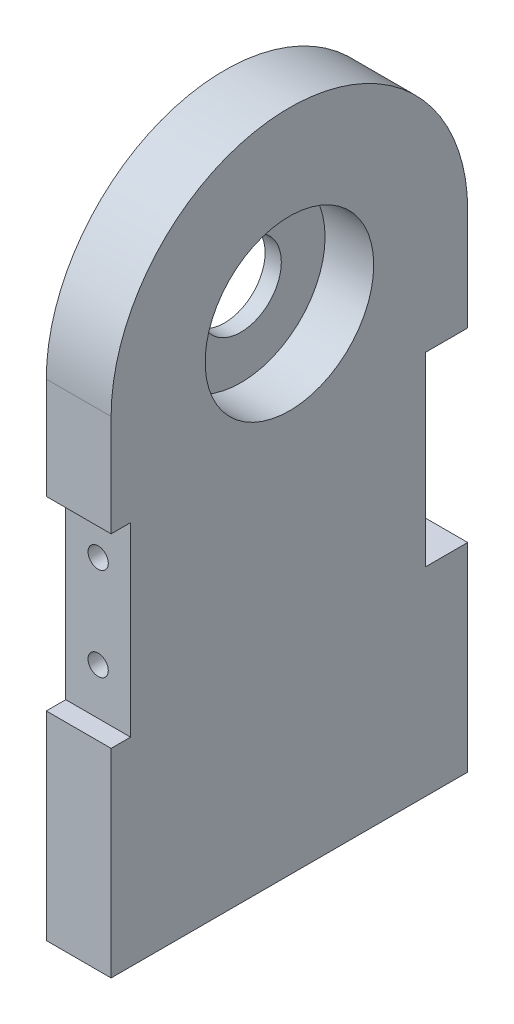
SolidWorks part; units mm, degrees
ref_plane "Front Plane" through (0, 0, 0) normal (0, 0, 1) x (1, 0, 0)
ref_plane "Top Plane" through (0, 0, 0) normal (0, 1, 0) x (1, 0, 0)
ref_plane "Right Plane" through (0, 0, 0) normal (1, 0, 0) x (0, 0, -1)
sketch "Sketch2" plane through (0, 0, 0) normal (1, 0, 0) x (0, 0, -1)
  line L1 (55, 75) -> (-55, 75)
  line L2 (55, 75) -> (55, -75)
  line L3 (55, -75) -> (-55, -75)
  line L4 (-55, 75) -> (-55, -75)
  line L5 (55, 75) -> (-55, -75) construction
  line L6 (55, -75) -> (-55, 75) construction
  circle A0 centre (0, 75) radius 55
  point P0 (0, 0)
  dimension "D1" = 110
  dimension "D2" = 150
extrude "Boss-Extrude1" add sketch "Sketch2" along normal blind 20 contours A0 L4 L3 L2 | L1 A0 | L1 A0
sketch "Sketch3" plane through (20, 0, 0) normal (1, 0, 0) x (0, 0, -1)
  circle A0 centre (0, 75) radius 26
  dimension "D1" = 52
extrude "Cut-Extrude1" cut sketch "Sketch3" against normal blind 15
sketch "Sketch4" plane through (5, 0, 0) normal (1, 0, 0) x (0, 0, -1)
  circle A0 centre (0, 75) radius 12.5
  dimension "D1" = 25
extrude "Cut-Extrude2" cut sketch "Sketch4" against normal blind 11.1125
sketch "Sketch5" plane through (0, -75, 0) normal (0, -1, 0) x (1, 0, 0)
  line L0 (10, 55) -> (10, -55) construction
  line L1 (20, 55) -> (0, 55) construction
  line L2 (20, -55) -> (0, -55) construction
  point P6 (10, 36.6667)
  point P7 (10, 18.3333)
  point P8 (10, 0)
  point P9 (10, -18.3333)
  point P10 (10, -36.6667)
hole_wizard "Tap Drill for M6x1.0 Tap2" positions "Sketch9" profile "Sketch10" hole size "M6x1.0" standard "ANSI Metric"
sketch "Sketch9" plane through (0, -75, 0) normal (0, -1, 0) x (-1, 0, 0)
  line L0 (-10, -55) -> (-10, 55) construction
  point P0 (-10, -36.6667)
  point P3 (-10, -18.3333)
  point P6 (-10, 0)
  point P10 (-10, 18.3333)
  point P13 (-10, 36.6667)
sketch "Sketch10" plane through (10, -75, 36.6667) normal (1, 0, 0) x (0, 0, -1)
  line L0 (0, 0) -> (0, 41.5022)
  line L1 (0, 41.5022) -> (2.5, 40)
  line L2 (2.5, 40) -> (2.5, 0)
  line L5 (2.5, 0) -> (0, 0)
  line L10 (0, 41.5022) -> (-2.5, 40) construction
  line L11 (0, -6.35) -> (0, 107.95) construction
  dimension "Hole Dia." = 5
  dimension "Hole Depth" = 40
  dimension "Drill Angle" = 118
sketch "Sketch11" plane through (0, 0, 0) normal (-1, 0, 0) x (0, 0, 1)
  line L0 (0, 35) -> (0, 15) construction
  line L1 (0, 75) -> (0, 35) construction
  line L2 (-55, 15) -> (55, 15) construction
  line L3 (55, 75) -> (55, -75) construction
  circle A0 centre (0, 75) radius 40 construction
  point P11 (0, 15)
  dimension "D1" = 80
  dimension "D2" = 20
sketch "Sketch12" plane through (20, 0, 0) normal (1, 0, 0) x (0, 0, -1)
  line L0 (-55, 43.65) -> (-55, -13.65)
  line L1 (55, 43.65) -> (42, 43.65)
  line L2 (-55, 75) -> (-55, -75) construction
  line L3 (-55, 43.65) -> (-49, 43.65)
  line L4 (-49, 43.65) -> (-49, -13.65)
  line L5 (-49, -13.65) -> (-55, -13.65)
  line L6 (55, 43.65) -> (55, -13.65)
  line L7 (42, 43.65) -> (42, -13.65)
  line L8 (55, 75) -> (55, -75) construction
  line L9 (42, -13.65) -> (55, -13.65)
  point P4 (-55, 15)
  point P13 (55, 15)
  dimension "D1" = 57.3
  dimension "D2" = 57.3
extrude "Cut-Extrude3" cut sketch "Sketch12" against normal blind 20
sketch "Sketch13" plane through (0, 0, 49) normal (0, 0, 1) x (1, 0, 0)
  line L0 (10, 43.65) -> (10, -13.65) construction
  line L1 (0, 43.65) -> (20, 43.65) construction
  line L2 (0, -13.65) -> (20, -13.65) construction
  point P6 (10, 29.325)
  point P7 (10, 15)
  point P8 (10, 0.675)
hole_wizard "Tap Drill for M6 Helicoil1" positions "3DSketch1" profile "Sketch14" hole size "M6x1.0" standard "ANSI Metric"
sketch3d "3DSketch1"
  point P0 (10, 29.325, 49)
  point P3 (10, 0.675, 49)
sketch "Sketch14" plane through (10, 29.325, 49) normal (1, 0, 0) x (0, -1, 0)
  line L0 (0, 0) -> (0, 21.8777)
  line L1 (0, 21.8777) -> (3.125, 20)
  line L2 (3.125, 20) -> (3.125, 0)
  line L5 (3.125, 0) -> (0, 0)
  line L10 (0, 21.8777) -> (-3.125, 20) construction
  line L11 (0, -6.35) -> (0, 107.95) construction
  dimension "Hole Dia." = 6.25
  dimension "Hole Depth" = 20
  dimension "Drill Angle" = 118
sketch "Sketch15" plane through (0, 0, -42) normal (0, 0, -1) x (-1, 0, 0)
  line L0 (-10, 43.65) -> (-10, -13.65) construction
  line L1 (0, 43.65) -> (-20, 43.65) construction
  line L2 (0, -13.65) -> (-20, -13.65) construction
  point P6 (-10, 29.325)
  point P7 (-10, 15)
  point P8 (-10, 0.675)
hole_wizard "Tap Drill for M6 Helicoil2" positions "Sketch16" profile "Sketch17" hole size "M6x1.0" standard "ANSI Metric"
sketch "Sketch16" plane through (0, 0, -42) normal (0, 0, -1) x (-1, 0, 0)
  point P0 (-10, 29.325)
  point P3 (-10, 0.675)
sketch "Sketch17" plane through (10, 29.325, -42) normal (1, 0, 0) x (0, 1, 0)
  line L0 (0, 0) -> (0, 21.8777)
  line L1 (0, 21.8777) -> (3.125, 20)
  line L2 (3.125, 20) -> (3.125, 0)
  line L5 (3.125, 0) -> (0, 0)
  line L10 (0, 21.8777) -> (-3.125, 20) construction
  line L11 (0, -6.35) -> (0, 107.95) construction
  dimension "Hole Dia." = 6.25
  dimension "Hole Depth" = 20
  dimension "Drill Angle" = 118
equation "\"GearDiameter\"= 80mm"
equation "\"WormGearDiam\"= 40mm"
equation "\"WormLength\"= 40mm"
equation "\"WormHubDiam\"= 25mm"
equation "\"D1@Sketch11\"=\"GearDiameter\""
equation "\"D2@Sketch11\"=\"WormGearDiam\" /2"
